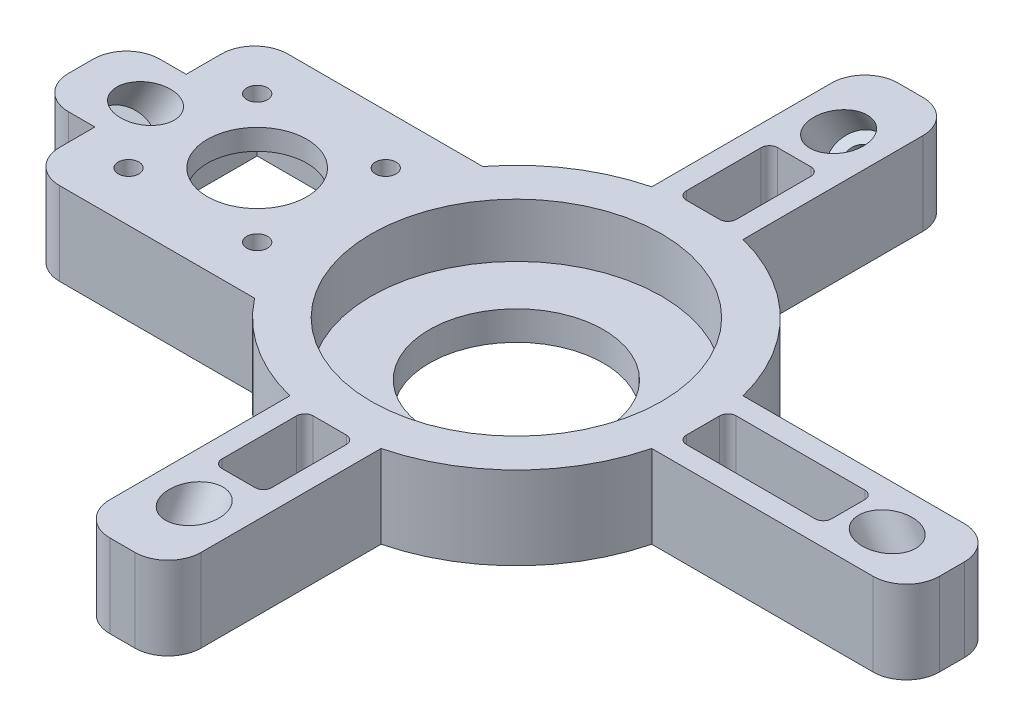
SolidWorks part; units mm, degrees
ref_plane "Спереди" through (0, 0, 0) normal (0, 0, 1) x (1, 0, 0)
ref_plane "Сверху" through (0, 0, 0) normal (0, 1, 0) x (1, 0, 0)
ref_plane "Справа" through (0, 0, 0) normal (1, 0, 0) x (0, 0, -1)
sketch "Эскиз1" plane through (0, 0, 0) normal (0, 1, 0) x (1, 0, 0)
  line L0 (-11, 43.6348) -> (-11, 95)
  line L1 (-11, 95) -> (11, 95)
  line L2 (11, 95) -> (11, 43.6348)
  line L3 (105, -11) -> (43.6348, -11)
  line L4 (43.6348, 11) -> (105, 11)
  line L5 (105, 11) -> (105, -11)
  line L6 (-11, -43.6348) -> (-11, -95)
  line L7 (11, -43.6348) -> (11, -95)
  line L8 (-11, -95) -> (11, -95)
  line L9 (-105, 11) -> (-43.6348, 11)
  line L10 (-43.6348, -11) -> (-105, -11)
  line L11 (-105, -11) -> (-105, 11)
  arc A0 (-43.6348, -11) -> (-11, -43.6348) centre (0, 0) ccw
  arc A1 (-11, 43.6348) -> (-43.6348, 11) centre (0, 0) ccw
  arc A2 (43.6348, 11) -> (11, 43.6348) centre (0, 0) ccw
  arc A3 (11, -43.6348) -> (43.6348, -11) centre (0, 0) ccw
  circle A4 centre (0, 0) radius 21
  point P6 (0, 95)
  point P8 (0, -95)
  point P10 (105, 0)
  point P11 (-105, 0)
  point P23 (0, 0)
  dimension "D1" = 190
  dimension "D2" = 42
  dimension "D4" = 45
  dimension "D3" = 22
  dimension "D6" = 210
extrude "Бобышка-Вытянуть1" add sketch "Эскиз1" along normal blind 20
sketch "Эскиз5" plane through (0, 20, 0) normal (0, 1, 0) x (1, 0, 0)
  line L0 (-35.6195, 27.5) -> (-90.6195, 27.5)
  line L1 (-90.6195, 27.5) -> (-90.6195, 11)
  line L2 (-43.6348, 11) -> (-105, 11) construction
  line L3 (-35.6195, -27.5) -> (-90.6195, -27.5)
  line L4 (-90.6195, -27.5) -> (-90.6195, -11)
  line L5 (-105, -11) -> (-43.6348, -11) construction
  line L6 (-90.6195, 11) -> (-43.6348, 11)
  line L7 (-90.6195, -11) -> (-43.6348, -11)
  arc A0 (-11, 43.6348) -> (-43.6348, 11) centre (0, 0) ccw construction
  arc A1 (-43.6348, -11) -> (-11, -43.6348) centre (0, 0) ccw construction
  arc A2 (-43.6348, 11) -> (-35.6195, 27.5) centre (0, 0) cw
  arc A3 (-43.6348, -11) -> (-35.6195, -27.5) centre (0, 0) ccw
  dimension "D1" = 55
  dimension "D2" = 55
extrude "Бобышка-Вытянуть2" add sketch "Эскиз5" against normal through all
sketch "Эскиз6" plane through (0, 20, 0) normal (0, 1, 0) x (1, 0, 0)
  circle A0 centre (0, 0) radius 35
  dimension "D1" = 70
extrude "Вырез-Вытянуть4" cut sketch "Эскиз6" against normal offset from surface (13 mm away) 7 up to face at (-17.0078, 0, 0)
sketch "Эскиз4" plane through (0, 20, 0) normal (0, 1, 0) x (1, 0, 0)
  line L0 (-78, 15.5) -> (-78, -15.5) construction
  line L1 (-78, 15.5) -> (-47, 15.5) construction
  circle A0 centre (-47, 15.5) radius 2.5
  circle A1 centre (-78, 15.5) radius 2.5
  circle A2 centre (-78, -15.5) radius 2.5
  circle A3 centre (-47, -15.5) radius 2.5
  circle A4 centre (-62.5, 0) radius 12
  point P10 (-62.5, 15.5)
  point P11 (-78, 0)
  dimension "D1" = 5
  dimension "D2" = 31
  dimension "D3" = 31
  dimension "D4" = 24
  dimension "D5" = 62.5
extrude "Вырез-Вытянуть3" cut sketch "Эскиз4" against normal through all
sketch "Эскиз7" plane through (0, 0, 0) normal (0, -1, 0) x (1, 0, 0)
  line L1 (-85, -22.5) -> (-40, -22.5)
  line L2 (-85, -22.5) -> (-85, 22.5)
  line L3 (-85, 22.5) -> (-40, 22.5)
  line L4 (-40, -22.5) -> (-40, 22.5)
  line L5 (-85, -22.5) -> (-40, 22.5) construction
  line L6 (-85, 22.5) -> (-40, -22.5) construction
  point P0 (-62.5, 0)
  dimension "D1" = 45
extrude "Вырез-Вытянуть5" cut sketch "Эскиз7" against normal offset from surface (15 mm away) 5 up to face at (-78, 20, -13)
ref_plane "Плоскость1" through (0, 19.7631, 11.4103) normal (0, 0.866, 0.5) x (1, 0, 0)
sketch "Эскиз2" plane through (0, 19.7631, 11.4103) normal (0, 0.866, 0.5) x (1, 0, 0)
  line L0 (11, 92.2724) -> (-11, 92.2724) construction
  circle A0 centre (0, 77.2724) radius 6
  dimension "D1" = 12
  dimension "D2" = 15
extrude "Вырез-Вытянуть1" cut sketch "Эскиз2" against normal blind 54
sketch "Эскиз3" plane through (0, -27.0022, -15.5897) normal (0, 0.866, 0.5) x (1, 0, 0)
  circle A0 centre (0, 77.2724) radius 3.1
  dimension "D1" = 6.2
extrude "Вырез-Вытянуть2" cut sketch "Эскиз3" against normal through all
ref_plane "Плоскость2" through (11.4103, 19.7631, 0) normal (0.5, 0.866, 0) x (0, 0, -1)
sketch "Эскиз8" plane through (11.4103, 19.7631, 0) normal (0.5, 0.866, 0) x (0, 0, -1)
  line L0 (11, 100.9327) -> (-11, 100.9327) construction
  circle A0 centre (0, 87.4327) radius 6
  dimension "D1" = 12
  dimension "D2" = 13.5
extrude "Вырез-Вытянуть6" cut sketch "Эскиз8" against normal blind 61
sketch "Эскиз9" plane through (-19.0897, -33.0644, 0) normal (0.5, 0.866, 0) x (0.866, -0.5, 0)
  circle A0 centre (-87.4327, 0) radius 3.1
  dimension "D1" = 6.2
extrude "Вырез-Вытянуть7" cut sketch "Эскиз9" against normal through all
fillet "Скругление1" radius 8 10 edges at (105, 10, -11) (105, 10, 11) (11, 10, 95) (-90.6195, 10, -27.5) (-90.6195, 10, 27.5) (-105, 10, 11) (-105, 10, -11) (11, 10, -95) (-11, 10, 95) (-11, 10, -95)
mirror "Зеркальное отражение1" about plane through (0, 0, 0) normal (0, 0, 1) of "Вырез-Вытянуть2", "Вырез-Вытянуть1"
mirror "Зеркальное отражение2" about plane through (0, 0, 0) normal (1, 0, 0) of "Вырез-Вытянуть7", "Вырез-Вытянуть6"
sketch "Эскиз10" plane through (0, 20, 0) normal (0, 1, 0) x (1, 0, 0)
  line L0 (-11, 87) -> (-11, 43.6348) construction
  line L1 (-6, 45) -> (6, 45)
  line L2 (-6, 45) -> (-6, 67)
  line L3 (-6, 67) -> (6, 67)
  line L4 (6, 45) -> (6, 67)
  line L5 (-6, 45) -> (6, 67) construction
  line L6 (-6, 67) -> (6, 45) construction
  line L7 (45, -6) -> (80, -6)
  line L8 (45, -6) -> (45, 6)
  line L9 (45, 6) -> (80, 6)
  line L10 (80, -6) -> (80, 6)
  line L11 (45, -6) -> (80, 6) construction
  line L12 (45, 6) -> (80, -6) construction
  line L13 (0, 0) -> (-25.4982, 0) construction
  line L14 (-6, -67) -> (6, -45) construction
  line L15 (-6, -45) -> (6, -67) construction
  line L16 (6, -45) -> (6, -67)
  line L17 (-6, -67) -> (6, -67)
  line L18 (-6, -45) -> (-6, -67)
  line L19 (11, 43.6348) -> (11, 87) construction
  line L20 (-6, -45) -> (6, -45)
  line L21 (97, 11) -> (43.6348, 11) construction
  line L22 (43.6348, -11) -> (97, -11) construction
  point P0 (0, 56)
  point P6 (62.5, 0)
  point P17 (0, -56)
  dimension "D1" = 45
  dimension "D2" = 5
  dimension "D3" = 5
  dimension "D4" = 22
  dimension "D5" = 45
  dimension "D6" = 5
  dimension "D7" = 5
  dimension "D8" = 35
extrude "Вырез-Вытянуть8" cut sketch "Эскиз10" against normal through all
fillet "Скругление2" radius 2 12 edges at (6, 10, 45) (-6, 10, 45) (6, 10, 67) (-6, 10, 67) (6, 10, -67) (-6, 10, -67) (-6, 10, -45) (6, 10, -45) (80, 10, -6) (80, 10, 6) (45, 10, -6) (45, 10, 6)
